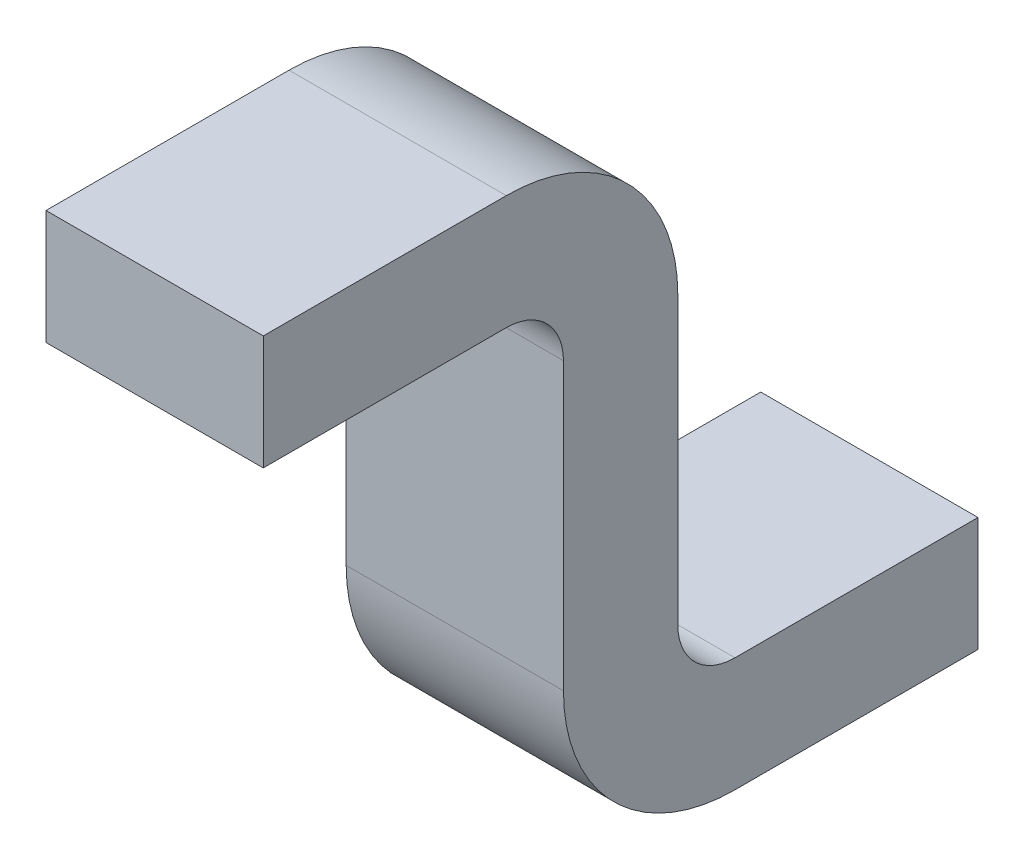
SolidWorks part; units mm, degrees
ref_plane "Front Plane" through (0, 0, 0) normal (0, 0, 1) x (1, 0, 0)
ref_plane "Top Plane" through (0, 0, 0) normal (0, 1, 0) x (1, 0, 0)
ref_plane "Right Plane" through (0, 0, 0) normal (1, 0, 0) x (0, 0, -1)
sketch "Sketch2" plane through (0, 0, 0) normal (1, 0, 0) x (0, 0, -1)
  line L0 (0, 0.9) -> (0.425, 0.9)
  line L1 (0.825, 0) -> (1.25, 0)
  line L2 (0, 0.9) -> (0, 1.1)
  line L3 (0, 1.1) -> (0.425, 1.1)
  line L4 (1.25, 0) -> (1.25, 0.2)
  line L6 (0.825, 0.2) -> (1.25, 0.2)
  line L7 (0.525, 0.8) -> (0.525, 0.3)
  line L8 (0.725, 0.8) -> (0.725, 0.3)
  arc A0 (0.525, 0.8) -> (0.425, 0.9) centre (0.425, 0.8) ccw
  arc A1 (0.825, 0.2) -> (0.725, 0.3) centre (0.825, 0.3) cw
  arc A2 (0.725, 0.8) -> (0.425, 1.1) centre (0.425, 0.8) ccw
  arc A3 (0.825, 0) -> (0.525, 0.3) centre (0.825, 0.3) cw
  dimension "D2" = 0.1
  dimension "D1" = 0.2
  dimension "D3" = 0.2
  dimension "D4" = 0.2
extrude "Extrude1" add sketch "Sketch2" along normal blind 0.38
